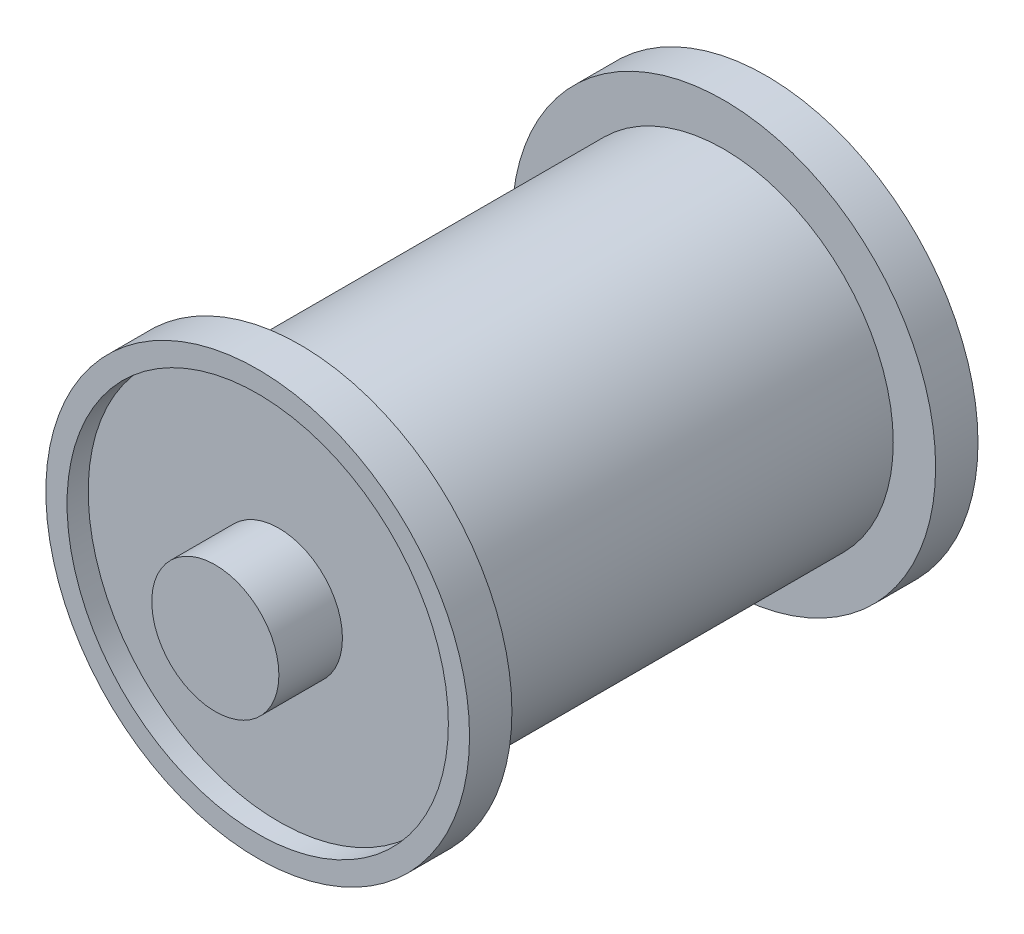
SolidWorks part; units mm, degrees
ref_plane "Alzado" through (0, 0, 0) normal (0, 0, 1) x (1, 0, 0)
ref_plane "Planta" through (0, 0, 0) normal (0, 1, 0) x (1, 0, 0)
ref_plane "Vista lateral" through (0, 0, 0) normal (1, 0, 0) x (0, 0, -1)
sketch "Croquis1" plane through (0, 0, 0) normal (0, 0, 1) x (1, 0, 0)
  circle A0 centre (0, 0) radius 10
  dimension "D1" = 20
extrude "Extruir1" add sketch "Croquis1" along normal blind 2
shell "Vaciado1" thickness 1
sketch "Croquis2" plane through (0, 0, 0) normal (0, 0, -1) x (-1, 0, 0)
  circle A0 centre (0, 0) radius 8
  dimension "D1" = 16
extrude "Extruir2" add sketch "Croquis2" along normal blind 10
mirror "Simetría3" about plane through (0, 0, -10) normal (0, 0, -1) of bodies 102
sketch "Croquis4" plane through (0, 0, 1) normal (0, 0, 1) x (1, 0, 0)
  circle A0 centre (0, 0) radius 3
extrude "Extruir4" add sketch "Croquis4" along normal blind 3
